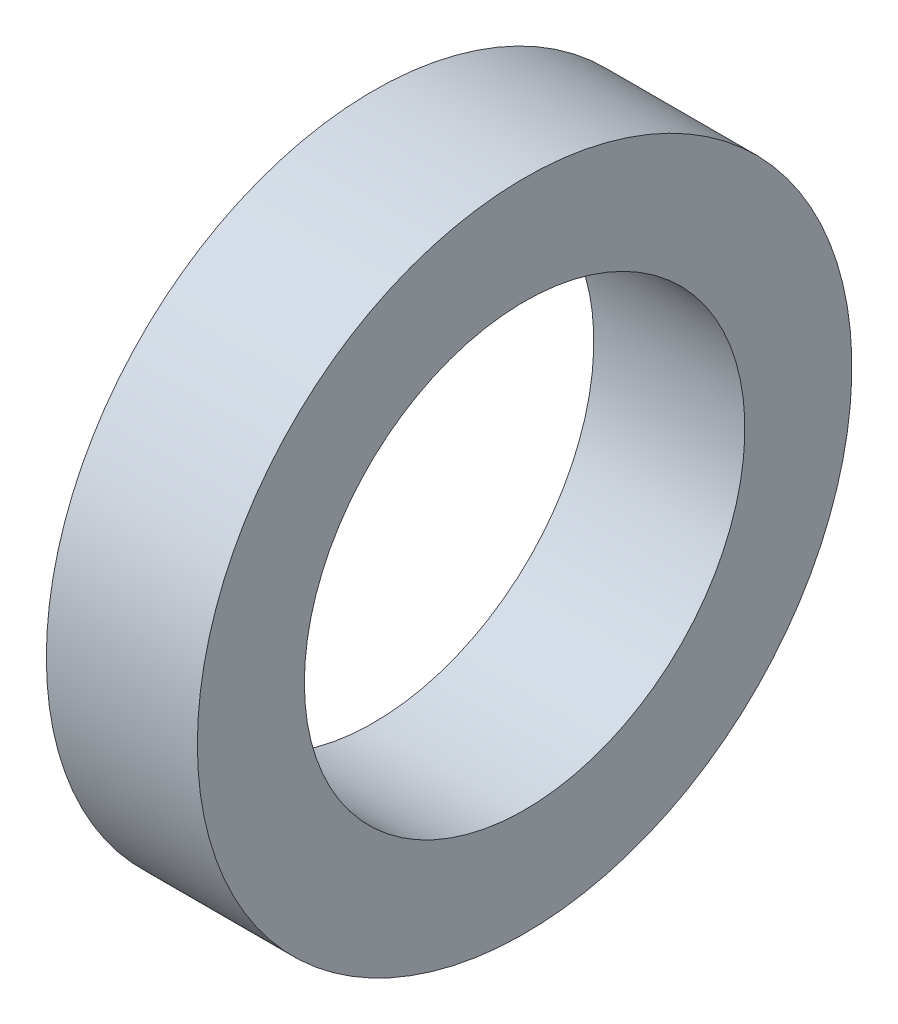
SolidWorks part; units mm, degrees
material "Plain Carbon Steel"
ref_plane "Front Plane" through (0, 0, 0) normal (0, 0, 1) x (1, 0, 0)
ref_plane "Top Plane" through (0, 0, 0) normal (0, 1, 0) x (1, 0, 0)
ref_plane "Right Plane" through (0, 0, 0) normal (1, 0, 0) x (0, 0, -1)
sketch "Sketch1" plane through (0, 0, 0) normal (0, 0, 1) x (1, 0, 0)
  line L0 (0, 0) -> (30.0376, 0) construction
  line L1 (0, 17.5) -> (12, 17.5)
  line L4 (12, 17.5) -> (12, 26)
  line L5 (12, 26) -> (0, 26)
  line L6 (0, 26) -> (0, 17.5)
  point P5 (0, 0)
  point P9 (0, 0)
  dimension "D1" = 35
  dimension "D3" = 12
  dimension "D4" = 52
revolve "Revolve1" add sketch "Sketch1" angle 360 about L0
